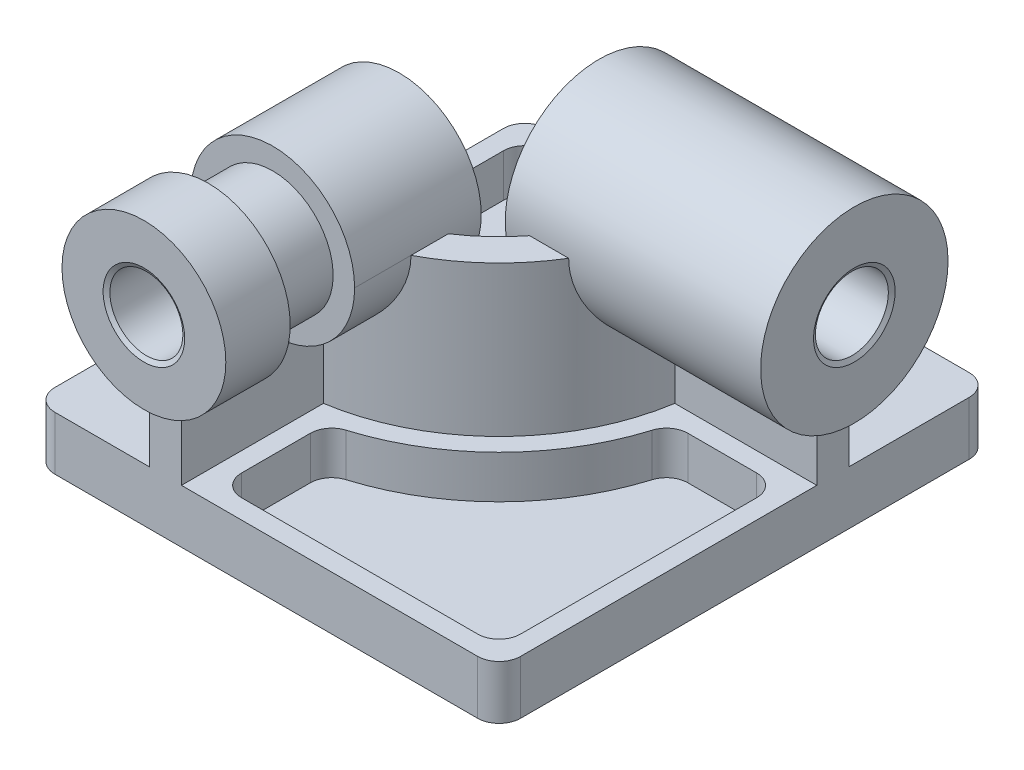
SolidWorks part; units mm, degrees
material "Alloy Steel"
ref_plane "Front Plane" through (0, 0, 0) normal (0, 0, 1) x (1, 0, 0)
ref_plane "Top Plane" through (0, 0, 0) normal (0, 1, 0) x (1, 0, 0)
ref_plane "Right Plane" through (0, 0, 0) normal (1, 0, 0) x (0, 0, -1)
sketch "Sketch1" plane through (0, 0, 0) normal (0, 1, 0) x (1, 0, 0)
  line L1 (0, 0) -> (-217, 0)
  line L2 (0, 0) -> (0, 229)
  line L3 (0, 229) -> (-217, 229)
  line L4 (-217, 0) -> (-217, 229)
  dimension "D1" = 217
  dimension "D2" = 229
extrude "Boss-Extrude1" add sketch "Sketch1" along normal blind 25
sketch "Sketch2" plane through (0, 25, 0) normal (0, 1, 0) x (1, 0, 0)
  line L0 (-163, 0) -> (-163, 80)
  line L1 (-217, 0) -> (0, 0) construction
  line L2 (-80, 163) -> (0, 163)
  line L3 (0, 0) -> (0, 229) construction
  arc A0 (-163, 80) -> (-80, 163) centre (-163, 163) ccw
  point P6 (0, 0)
  dimension "D1" = 163
  dimension "D2" = 163
  dimension "D3" = 80
extrude "Extrude-Thin1" add sketch "Sketch2" along normal blind 95 from surface at -25 thin
fillet "Fillet1" radius 10 4 edges at (0, 12.5, -229) (-217, 12.5, -229) (-217, 12.5, 0) (0, 12.5, 0)
sketch "Sketch9" plane through (0, 25, 0) normal (0, 1, 0) x (1, 0, 0)
  line L14 (-139, 9) -> (-10, 9)
  line L15 (-9, 10) -> (-9, 139)
  line L16 (-9, 139) -> (-58.7263, 139)
  line L17 (-139, 58.7263) -> (-139, 9)
  line L24 (-129, 9) -> (-19, 9)
  line L25 (-9, 19) -> (-9, 129)
  line L26 (-19, 139) -> (-51.0491, 139)
  line L27 (-139, 51.0491) -> (-139, 19)
  arc A12 (-9, 129) -> (-19, 139) centre (-19, 129) ccw
  arc A13 (-51.0491, 139) -> (-60.6176, 131.906) centre (-51.0491, 129) ccw
  arc A14 (-10, 9) -> (-9, 10) centre (-10, 10) ccw
  arc A15 (-139, 58.7263) -> (-58.7263, 139) centre (-163, 163) ccw
  arc A17 (-131.906, 60.6176) -> (-60.6176, 131.906) centre (-163, 163) ccw
  arc A18 (-129, 9) -> (-139, 19) centre (-129, 19) cw
  arc A19 (-131.906, 60.6176) -> (-139, 51.0491) centre (-129, 51.0491) ccw
  arc A20 (-19, 9) -> (-9, 19) centre (-19, 19) ccw
  point P14 (-9, 9)
  point P17 (0, 0)
  dimension "D2" = 10
  dimension "D3" = 10
  dimension "D1" = 9
extrude "Cut-Extrude1" cut sketch "Sketch9" against normal offset from surface (20 mm away) 5 up to face at (-108.5, 0, -114.5)
sketch "Sketch10" plane through (0, 0, 0) normal (0, 0, 1) x (1, 0, 0)
  line L0 (-148, 95) -> (-163, 95) construction
  circle A1 centre (-155.5, 95) radius 38.1667
  dimension "D2" = 76.3333
extrude "Boss-Extrude3" add sketch "Sketch10" against normal blind 119 from offset 10
sketch "Sketch11" plane through (0, 0, 10) normal (0, 0, 1) x (1, 0, 0)
  circle A2 centre (-155.5, 95) radius 17
  circle A3 centre (-155.5, 95) radius 38.1667
  circle A4 centre (-155.5, 95) radius 38.1667
  dimension "D2" = 34
  dimension "D1" = 0
extrude "Cut-Extrude2" cut sketch "Sketch11" against normal up to surface (119 mm away) contours A2 up to face at (-117.3333, 95, -109)
sketch "Sketch12" plane through (0, 0, 0) normal (1, 0, 0) x (0, 0, -1)
  line L0 (163, 95) -> (148, 95) construction
  circle A0 centre (155.5, 95) radius 43.6667
  dimension "D1" = 87.3333
extrude "Boss-Extrude4" add sketch "Sketch12" against normal blind 119 from offset 10
sketch "Sketch13" plane through (10, 0, 0) normal (1, 0, 0) x (0, 0, -1)
  circle A0 centre (155.5, 95) radius 17
  circle A1 centre (155.5, 95) radius 43.6667
  circle A2 centre (155.5, 95) radius 43.6667
  dimension "D2" = 34
  dimension "D1" = 0
extrude "Cut-Extrude3" cut sketch "Sketch13" against normal up to surface (119 mm away) contours A0 up to face at (-109, 95, -199.1667)
chamfer "Chamfer1" distance 2 angle 30 4 edges at (10, 95, -172.5) (-109, 95, -172.5) (-138.5, 95, 10) (-138.5, 95, -109)
sketch "Sketch15" plane through (0, 25, 0) normal (0, 1, 0) x (1, 0, 0)
  line L0 (-89, 163) -> (-89, 210)
  line L4 (-198, 89) -> (-163, 89)
  line L6 (-99, 220) -> (-198, 220)
  line L7 (-208, 210) -> (-208, 99)
  line L8 (-10, 229) -> (-207, 229) construction
  line L9 (-217, 219) -> (-217, 10) construction
  arc A3 (-163, 89) -> (-89, 163) centre (-163, 163) ccw
  arc A4 (-163, 89) -> (-89, 163) centre (-163, 163) ccw
  arc A5 (-208, 99) -> (-198, 89) centre (-198, 99) ccw
  arc A6 (-99, 220) -> (-89, 210) centre (-99, 210) cw
  arc A7 (-198, 220) -> (-208, 210) centre (-198, 210) ccw
  dimension "D4" = 10
  dimension "D2" = 9
  dimension "D3" = 9
  dimension "D1" = 9
extrude "Cut-Extrude4" cut sketch "Sketch15" against normal offset from surface (20 mm away) 5 up to face at (-108.5, 0, -114.5)
sketch "Sketch16" plane through (0, 0, 10) normal (0, 0, 1) x (1, 0, 0)
  circle A0 centre (-155.5, 95) radius 38.1667 construction
  circle A3 centre (-155.5, 95) radius 38.1667
  circle A6 centre (-155.5, 95) radius 28.1667
  circle M8 centre (-155.5, 95) radius 38.1667
  dimension "D1" = 10
extrude "Cut-Extrude5" cut sketch "Sketch16" against normal blind 30 from offset 30 contours A6 M8 offset against normal yes
sketch "Sketch17" plane through (0, 25, 0) normal (0, 1, 0) x (1, 0, 0)
  line L4 (-148, 50) -> (-163, 50)
  line L5 (-163, 50) -> (-163, 20)
  line L6 (-163, 20) -> (-148, 20)
  line L7 (-148, 20) -> (-148, 50)
  line L8 (-148, 50) -> (-163, 50)
  line L9 (-163, 50) -> (-163, 20)
  line L10 (-163, 20) -> (-148, 20)
  line L11 (-148, 20) -> (-148, 50)
  dimension "D1" = 0
extrude "Boss-Extrude5" add sketch "Sketch17" along normal up to surface (42.8502 mm away)
equation "\"A\" = 229"
equation "\"B\" = 217"
equation "\"C\" = 163"
equation "\"D\" = 119"
equation "\"E\" = 34"
equation "\"X\"= \"A\" / 3"
equation "\"Y\" = \"B\" / 3 + 15"
equation "\"D1@Sketch1\"=\"B\""
equation "\"D2@Sketch1\"=\"A\""
equation "\"D1@Sketch2\"=\"C\""
equation "\"D2@Sketch2\"=\"C\""
equation "\"D2@Sketch10\"=\"X\""
equation "\"D1@Boss-Extrude3\"=\"D\""
equation "\"D1@Sketch12\"=\"Y\""
equation "\"D1@Boss-Extrude4\"=\"D\""
equation "\"D2@Sketch13\"=\"E\""
equation "\"D2@Sketch11\"=\"E\""
